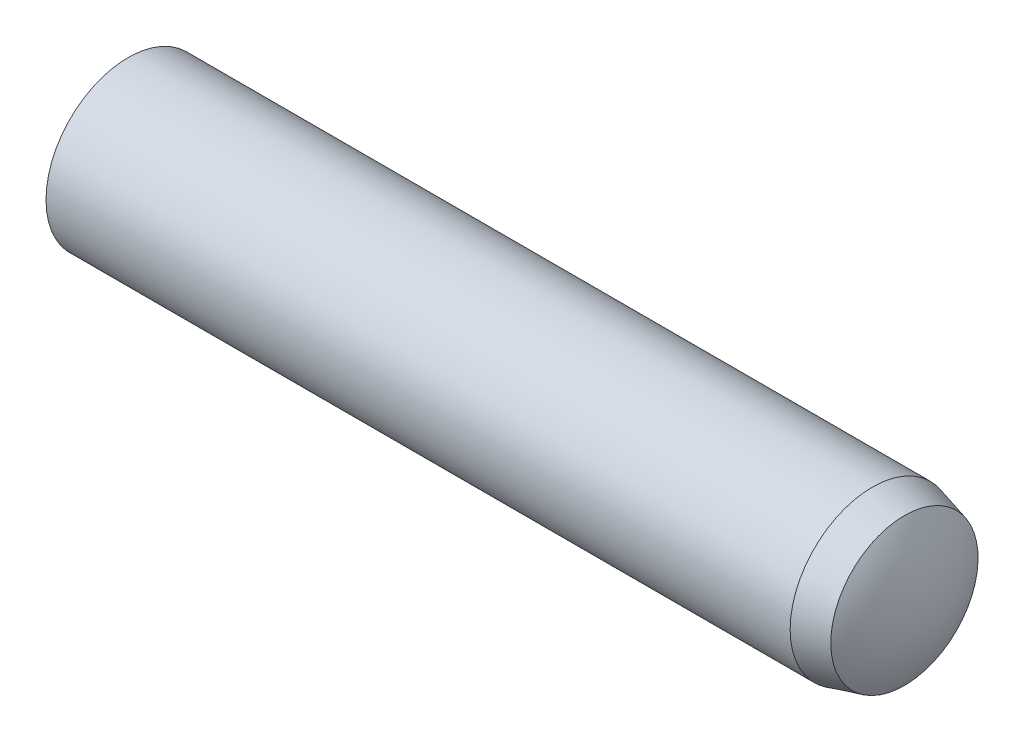
SolidWorks part; units mm, degrees
ref_plane "Front Plane" through (0, 0, 0) normal (0, 0, 1) x (1, 0, 0)
ref_plane "Top Plane" through (0, 0, 0) normal (0, 1, 0) x (1, 0, 0)
ref_plane "Right Plane" through (0, 0, 0) normal (1, 0, 0) x (0, 0, -1)
sketch "Sketch1" plane through (0, 0, 0) normal (0, 0, 1) x (1, 0, 0)
  line L0 (-5, 0) -> (5, 0) construction
  line L1 (5, 1) -> (5, -1) construction
  line L2 (-5, 1) -> (-5, -1) construction
  line L3 (4.35, 1) -> (4.35, -1) construction
  line L4 (-4.7, 1) -> (-4.7, -1) construction
  line L5 (-5, 0) -> (-4.7, 0) construction
  line L6 (5, 0) -> (4.35, 0) construction
  line L7 (4.74, 1) -> (4.74, -1) construction
  dimension "D1" = 0.65
  dimension "Dia" = 2
  dimension "D2" = 0.3
  dimension "Length" = 10
  dimension "D3" = 0.39
sketch "Sketch2" plane through (0, 0, 0) normal (1, 0, 0) x (0, 0, -1)
  circle A0 centre (0, 0) radius 1
extrude "Extrude1" add sketch "Sketch2" against normal up to vertex (5 mm away) and the other way up to vertex (5 mm away) up to point (-5, 0, 0) other way up to point (5, 0, 0)
sketch "Sketch5" plane through (0, 0, 0) normal (0, 0, 1) x (1, 0, 0)
  line L0 (4.35, 1) -> (4.35, 1.5)
  line L1 (4.35, 1.5) -> (5.5, 1.5)
  line L2 (5.5, 1.5) -> (5.5, 0)
  line L3 (5, 0) -> (5.5, 0)
  line L5 (-4.7, 1) -> (-4.7, 1.5)
  line L6 (-4.7, 1.5) -> (-5.5, 1.5)
  line L7 (-5.5, 1.5) -> (-5.5, 0)
  line L8 (4.35, 1) -> (4.74, 0.8955)
  line L10 (-5, 0) -> (-5.5, 0)
  line L11 (-5, 1) -> (-5, -1) construction
  line L13 (4.35, 1) -> (4.35, -1) construction
  line L15 (-5, 0) -> (5, 0) construction
  line L16 (4.74, 1) -> (4.74, -1) construction
  line L17 (5, 1) -> (5, -1) construction
  arc A0 (4.74, 0.8955) -> (5, 0) centre (3.3278, 0) cw
  arc A1 (-4.7, 1) -> (-5, 0) centre (-3.1833, 0) ccw
  dimension "D1" = 15
  dimension "D2" = 0.5
revolve "Cut-Revolve1" cut sketch "Sketch5" angle 360 about L0
equation "\"D1@Sketch1\" = \"Dia@Sketch1\"*.325"
equation "\"D2@Sketch1\" = \"Dia@Sketch1\"*.15"
equation "\"D3@Sketch1\" = \"D1@Sketch1\"*.6"
